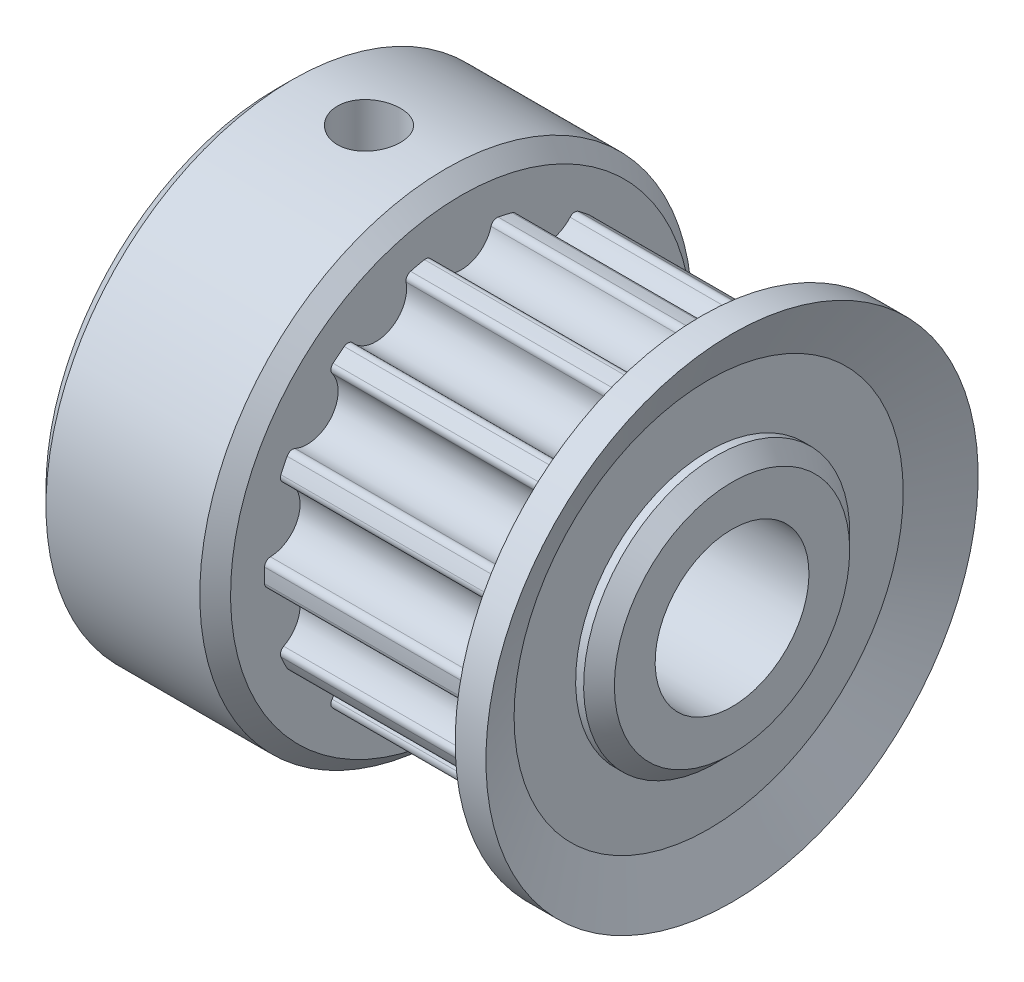
SolidWorks part; units mm, degrees
material "6061 Alloy"
ref_plane "Front Plane" through (0, 0, 0) normal (0, 0, 1) x (1, 0, 0)
ref_plane "Top Plane" through (0, 0, 0) normal (0, 1, 0) x (1, 0, 0)
ref_plane "Right Plane" through (0, 0, 0) normal (1, 0, 0) x (0, 0, -1)
sketch "Sketch5" plane through (0, 0, 0) normal (0, 0, 1) x (1, 0, 0)
  line L0 (0, 0) -> (0, 3.5)
  line L1 (0, 3.5) -> (0.3, 3.8)
  line L2 (0.3, 3.8) -> (0, 3.8)
  line L3 (0, 3.8) -> (0, 7.5)
  line L4 (0, 7.5) -> (0.5, 8)
  line L5 (0.5, 8) -> (5.5, 8)
  line L6 (5.5, 8) -> (6, 7.5)
  line L7 (6, 7.5) -> (6, 6.4)
  line L8 (6, 6.4) -> (13, 6.4)
  line L9 (13, 6.4) -> (13.8, 8)
  line L10 (13.8, 8) -> (14.8, 8)
  line L11 (14.8, 8) -> (14.04, 6.3243)
  line L12 (14.04, 6.3243) -> (14.04, 4.3243)
  line L13 (14.04, 4.3243) -> (14.3, 4.3243)
  line L14 (14.3, 4.3243) -> (14.8, 3.8243)
  line L15 (14.8, 3.8243) -> (14.8, 0)
  line L16 (14.8, 0) -> (0, 0)
  dimension "D1" = 8
  dimension "D2" = 14.8
  dimension "D3" = 14.8
  dimension "D4" = 0.5
  dimension "D5" = 0.5
  dimension "D6" = 5
  dimension "D7" = 3.5
  dimension "D8" = 0.3
  dimension "D9" = 0.3
  dimension "D10" = 6.4
  dimension "D11" = 1
  dimension "D12" = 7
  dimension "D13" = 0.5
  dimension "D14" = 0.5
  dimension "D15" = 0.26
  dimension "D16" = 2
  dimension "D17" = 1.84
revolve "Revolve2" add sketch "Sketch5" angle 360 about L16
sketch "Sketch6" plane through (14.8, 0, 0) normal (1, 0, 0) x (0, 0, -1)
  circle A0 centre (0, 0) radius 2.5
  dimension "D1" = 5
extrude "Cut-Extrude3" cut sketch "Sketch6" against normal through all
sketch "Sketch7" plane through (6, 0, 0) normal (1, 0, 0) x (0, 0, -1)
  circle A0 centre (0, 0) radius 6.4 construction
  circle A1 centre (0, 0) radius 6.4 construction
  circle A2 centre (0, 6.4) radius 1
  dimension "D1" = 2
extrude "Cut-Extrude4" cut sketch "Sketch7" along normal blind 7
fillet "Fillet2" radius 0.2 2 edges at (9.5, 6.3219, 0.9969) (9.5, 6.3219, -0.9969)
pattern_circular "CirPattern3" count 14 over 360 about axis through (0, 0, 0) along (1, 0, 0) of "Cut-Extrude4", "Fillet2"
ref_plane "Plane1" through (0, 8, 0) normal (0, 1, 0) x (1, 0, 0)
hole_wizard "M2.5 Tapped Hole1" positions "Sketch9" profile "Sketch10" tap size "M2.5" standard "ISO"
sketch "Sketch9" plane through (0, 8, 0) normal (0, 1, 0) x (1, 0, 0)
  line L0 (3, 8) -> (3, 0) construction
  line L1 (5.5, 8) -> (0.5, 8) construction
  point P0 (3, 0)
sketch "Sketch10" plane through (3, 8, 0) normal (1, 0, 0) x (0, 0, 1)
  line L0 (0, 0) -> (0, 5.5)
  line L1 (0, 5.5) -> (1.025, 5.5)
  line L2 (1.025, 5.5) -> (1.025, 0)
  line L5 (1.025, 0) -> (0, 0)
  line L11 (0, -6.35) -> (0, 107.95) construction
  dimension "Thru Tap Drill Dia." = 2.05
  dimension "Thru Tap Drill Depth" = 5.5
cosmetic thread "Hole Thread1" parameters "D2"=2.5
